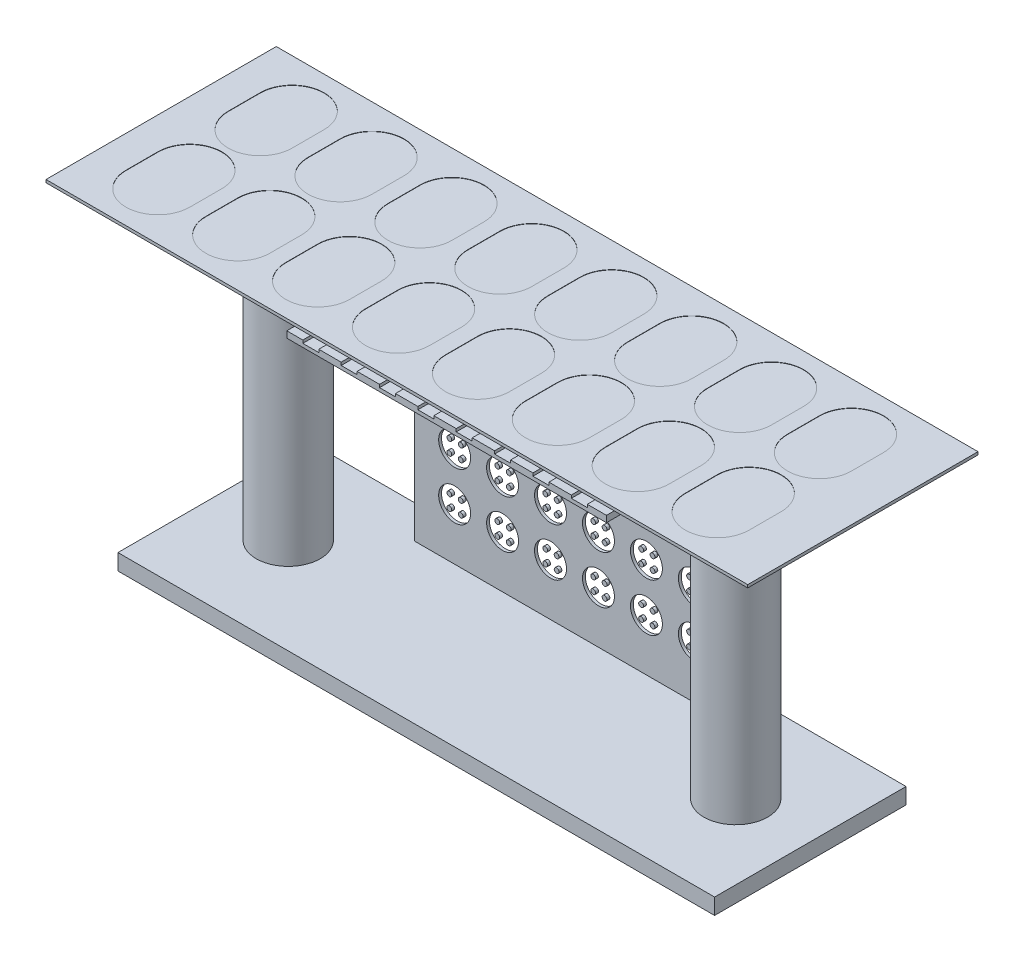
SolidWorks part; units mm, degrees
ref_plane "Front Plane" through (0, 0, 0) normal (0, 0, 1) x (1, 0, 0)
ref_plane "Top Plane" through (0, 0, 0) normal (0, 1, 0) x (1, 0, 0)
ref_plane "Right Plane" through (0, 0, 0) normal (1, 0, 0) x (0, 0, -1)
sketch "Sketch3" plane through (0, 0, 0) normal (0, 0, 1) x (1, 0, 0)
  line L1 (-5000, 4000) -> (5000, 4000)
  line L2 (-5000, 4000) -> (-5000, -4000)
  line L3 (-5000, -4000) -> (5000, -4000)
  line L4 (5000, 4000) -> (5000, -4000)
  line L5 (-5000, 4000) -> (5000, -4000) construction
  line L6 (-5000, -4000) -> (5000, 4000) construction
  point P0 (0, 0)
  dimension "D1" = 8000
  dimension "D2" = 10000
extrude "Boss-Extrude1" add sketch "Sketch3" along normal blind 90
ref_plane "Plane2" through (0, 4000, 0) normal (0, 1, 0) x (1, 0, 0)
sketch "Sketch6" plane through (0, 4000, 0) normal (0, 1, 0) x (1, 0, 0)
  line L0 (-5000, -90) -> (-5000, -4090)
  line L1 (-5000, -4090) -> (5000, -4090)
  line L2 (5000, -4090) -> (5000, -90)
  line L3 (5000, -90) -> (-5000, -90)
  dimension "D1" = 4000
extrude "Boss-Extrude2" add sketch "Sketch6" along normal blind 200 separate body
sketch "Sketch7" plane through (0, 0, 90) normal (0, 0, 1) x (1, 0, 0)
  line L0 (-5000, 4000) -> (-5000, -4000) construction
  line L1 (-3750, 2623.5986) -> (-3750, 1123.5986) construction
  circle A0 centre (-3750, 2623.5986) radius 500
  circle A1 centre (-3915.8517, 2823.5986) radius 75
  circle A2 centre (-3559.1798, 2823.5986) radius 75
  circle A3 centre (-3559.1798, 2423.5986) radius 75
  circle A4 centre (-3915.8517, 2423.5986) radius 75
  circle A5 centre (-2250, 2623.5986) radius 500
  circle A6 centre (-2415.8517, 2423.5986) radius 75
  circle A7 centre (-2059.1798, 2823.5986) radius 75
  circle A8 centre (-2059.1798, 2423.5986) radius 75
  circle A9 centre (-2415.8517, 2823.5986) radius 75
  circle A10 centre (-750, 2623.5986) radius 500
  circle A11 centre (-915.8517, 2423.5986) radius 75
  circle A12 centre (-559.1798, 2823.5986) radius 75
  circle A13 centre (-559.1798, 2423.5986) radius 75
  circle A14 centre (-915.8517, 2823.5986) radius 75
  circle A15 centre (750, 2623.5986) radius 500
  circle A16 centre (584.1483, 2423.5986) radius 75
  circle A17 centre (940.8202, 2823.5986) radius 75
  circle A18 centre (940.8202, 2423.5986) radius 75
  circle A19 centre (584.1483, 2823.5986) radius 75
  circle A20 centre (2250, 2623.5986) radius 500
  circle A21 centre (2084.1483, 2423.5986) radius 75
  circle A22 centre (2440.8202, 2823.5986) radius 75
  circle A23 centre (2440.8202, 2423.5986) radius 75
  circle A24 centre (2084.1483, 2823.5986) radius 75
  circle A25 centre (3750, 2623.5986) radius 500
  circle A26 centre (3584.1483, 2423.5986) radius 75
  circle A27 centre (3940.8202, 2823.5986) radius 75
  circle A28 centre (3940.8202, 2423.5986) radius 75
  circle A29 centre (3584.1483, 2823.5986) radius 75
  circle A30 centre (-2250, 1123.5986) radius 500
  circle A31 centre (-2415.8517, 923.5986) radius 75
  circle A32 centre (-2059.1798, 1323.5986) radius 75
  circle A33 centre (-2059.1798, 923.5986) radius 75
  circle A34 centre (-2415.8517, 1323.5986) radius 75
  circle A35 centre (-750, 1123.5986) radius 500
  circle A36 centre (-915.8517, 923.5986) radius 75
  circle A37 centre (-559.1798, 1323.5986) radius 75
  circle A38 centre (-559.1798, 923.5986) radius 75
  circle A39 centre (-915.8517, 1323.5986) radius 75
  circle A40 centre (750, 1123.5986) radius 500
  circle A41 centre (584.1483, 923.5986) radius 75
  circle A42 centre (940.8202, 1323.5986) radius 75
  circle A43 centre (940.8202, 923.5986) radius 75
  circle A44 centre (584.1483, 1323.5986) radius 75
  circle A45 centre (2250, 1123.5986) radius 500
  circle A46 centre (2084.1483, 923.5986) radius 75
  circle A47 centre (2440.8202, 1323.5986) radius 75
  circle A48 centre (2440.8202, 923.5986) radius 75
  circle A49 centre (2084.1483, 1323.5986) radius 75
  circle A50 centre (3750, 1123.5986) radius 500
  circle A51 centre (3584.1483, 923.5986) radius 75
  circle A52 centre (3940.8202, 1323.5986) radius 75
  circle A53 centre (3940.8202, 923.5986) radius 75
  circle A54 centre (3584.1483, 1323.5986) radius 75
  circle A55 centre (-2250, -376.4014) radius 500
  circle A56 centre (-2415.8517, -576.4014) radius 75
  circle A57 centre (-2059.1798, -176.4014) radius 75
  circle A58 centre (-2059.1798, -576.4014) radius 75
  circle A59 centre (-2415.8517, -176.4014) radius 75
  circle A60 centre (-750, -376.4014) radius 500
  circle A61 centre (-915.8517, -576.4014) radius 75
  circle A62 centre (-559.1798, -176.4014) radius 75
  circle A63 centre (-559.1798, -576.4014) radius 75
  circle A64 centre (-915.8517, -176.4014) radius 75
  circle A65 centre (750, -376.4014) radius 500
  circle A66 centre (584.1483, -576.4014) radius 75
  circle A67 centre (940.8202, -176.4014) radius 75
  circle A68 centre (940.8202, -576.4014) radius 75
  circle A69 centre (584.1483, -176.4014) radius 75
  circle A70 centre (2250, -376.4014) radius 500
  circle A71 centre (2084.1483, -576.4014) radius 75
  circle A72 centre (2440.8202, -176.4014) radius 75
  circle A73 centre (2440.8202, -576.4014) radius 75
  circle A74 centre (2084.1483, -176.4014) radius 75
  circle A75 centre (3750, -376.4014) radius 500
  circle A76 centre (3584.1483, -576.4014) radius 75
  circle A77 centre (3940.8202, -176.4014) radius 75
  circle A78 centre (3940.8202, -576.4014) radius 75
  circle A79 centre (3584.1483, -176.4014) radius 75
  circle A80 centre (-2250, -1876.4014) radius 500
  circle A81 centre (-2415.8517, -2076.4014) radius 75
  circle A82 centre (-2059.1798, -1676.4014) radius 75
  circle A83 centre (-2059.1798, -2076.4014) radius 75
  circle A84 centre (-2415.8517, -1676.4014) radius 75
  circle A85 centre (-750, -1876.4014) radius 500
  circle A86 centre (-915.8517, -2076.4014) radius 75
  circle A87 centre (-559.1798, -1676.4014) radius 75
  circle A88 centre (-559.1798, -2076.4014) radius 75
  circle A89 centre (-915.8517, -1676.4014) radius 75
  circle A90 centre (750, -1876.4014) radius 500
  circle A91 centre (584.1483, -2076.4014) radius 75
  circle A92 centre (940.8202, -1676.4014) radius 75
  circle A93 centre (940.8202, -2076.4014) radius 75
  circle A94 centre (584.1483, -1676.4014) radius 75
  circle A95 centre (2250, -1876.4014) radius 500
  circle A96 centre (2084.1483, -2076.4014) radius 75
  circle A97 centre (2440.8202, -1676.4014) radius 75
  circle A98 centre (2440.8202, -2076.4014) radius 75
  circle A99 centre (2084.1483, -1676.4014) radius 75
  circle A100 centre (3750, -1876.4014) radius 500
  circle A101 centre (3584.1483, -2076.4014) radius 75
  circle A102 centre (3940.8202, -1676.4014) radius 75
  circle A103 centre (3940.8202, -2076.4014) radius 75
  circle A104 centre (3584.1483, -1676.4014) radius 75
  circle A105 centre (-3750, 1123.5986) radius 500
  circle A106 centre (-3915.8517, 923.5986) radius 75
  circle A107 centre (-3559.1798, 1323.5986) radius 75
  circle A108 centre (-3559.1798, 923.5986) radius 75
  circle A109 centre (-3915.8517, 1323.5986) radius 75
  circle A110 centre (-3750, -376.4014) radius 500
  circle A111 centre (-3915.8517, -576.4014) radius 75
  circle A112 centre (-3559.1798, -176.4014) radius 75
  circle A113 centre (-3559.1798, -576.4014) radius 75
  circle A114 centre (-3915.8517, -176.4014) radius 75
  circle A115 centre (-3750, -1876.4014) radius 500
  circle A116 centre (-3915.8517, -2076.4014) radius 75
  circle A117 centre (-3559.1798, -1676.4014) radius 75
  circle A118 centre (-3559.1798, -2076.4014) radius 75
  circle A119 centre (-3915.8517, -1676.4014) radius 75
  dimension "D5" = 150
  dimension "D6" = 150
  dimension "D7" = 150
  dimension "D8" = 150
  dimension "D10" = 1000
  dimension "D1" = 200
  dimension "D2" = 200
  dimension "D3" = 200
  dimension "D4" = 200
  dimension "D9" = 1250
  dimension "D13" = 1500
  dimension "D11" = 6
  dimension "D12" = 4
extrude "Cut-Extrude4" cut sketch "Sketch7" against normal through all contours A0 | A4 | A3 | A2 | A1
pattern_linear "LPattern1" count 6 spacing 1500 along (1, 0, 0) count 4 spacing 1500 along (0, -1, 0) of "Cut-Extrude4"
ref_plane "Plane3" through (0, -4000, 0) normal (0, 1, 0) x (1, 0, 0)
sketch "Sketch11" plane through (0, -4000, 0) normal (0, 1, 0) x (1, 0, 0)
  line L0 (-5000, -90) -> (-5000, -4090) construction
  line L1 (5000, -4090) -> (5000, -90) construction
  circle A0 centre (7000, -2045) radius 1000
  circle A1 centre (-7000, -2045) radius 1000
  dimension "D3" = 2000
  dimension "D4" = 2000
  dimension "D1" = 2000
  dimension "D2" = 2000
extrude "Boss-Extrude3" add sketch "Sketch11" along normal blind 10000 separate body
sketch "Sketch13" plane through (0, -4000, 0) normal (0, 1, 0) x (1, 0, 0)
  line L1 (-9333.4186, 950.2518) -> (9333.4186, 950.2518)
  line L2 (-9333.4186, 950.2518) -> (-9333.4186, -5040.2518)
  line L3 (-9333.4186, -5040.2518) -> (9333.4186, -5040.2518)
  line L4 (9333.4186, 950.2518) -> (9333.4186, -5040.2518)
  line L5 (-9333.4186, 950.2518) -> (9333.4186, -5040.2518) construction
  line L6 (-9333.4186, -5040.2518) -> (9333.4186, 950.2518) construction
  point P0 (0, -2045)
extrude "Boss-Extrude4" add sketch "Sketch13" along normal blind 500
sketch "Sketch14" plane through (0, 4200, 0) normal (0, 1, 0) x (1, 0, 0)
  line L0 (5000, -90) -> (-5000, -90) construction
  line L1 (-4500, -90) -> (-4000, -90)
  line L2 (-4500, -90) -> (-4500, -4090)
  line L3 (-4500, -4090) -> (-4000, -4090)
  line L4 (-4000, -90) -> (-4000, -4090)
  line L5 (-5000, -4090) -> (5000, -4090) construction
  line L6 (-5000, -90) -> (-5000, -4090) construction
  dimension "D1" = 500
  dimension "D2" = 500
extrude "Cut-Extrude5" cut sketch "Sketch14" against normal blind 90 contours L2 L3 L4 L1
pattern_linear "LPattern2" count 8 spacing 1200 along (1, 0, 0) of "Cut-Extrude5"
sketch "Sketch17" plane through (0, 6000, 0) normal (0, 1, 0) x (1, 0, 0)
  line L1 (-10977.0173, 1557.277) -> (10977.0173, 1557.277)
  line L2 (-10977.0173, 1557.277) -> (-10977.0173, -5647.277)
  line L3 (-10977.0173, -5647.277) -> (10977.0173, -5647.277)
  line L4 (10977.0173, 1557.277) -> (10977.0173, -5647.277)
  line L5 (-10977.0173, 1557.277) -> (10977.0173, -5647.277) construction
  line L6 (-10977.0173, -5647.277) -> (10977.0173, 1557.277) construction
  point P0 (0, -2045)
  dimension "D1" = 7204.554
extrude "Boss-Extrude5" add sketch "Sketch17" along normal blind 90
sketch "Sketch19" plane through (0, 6090, 0) normal (0, 1, 0) x (1, 0, 0)
  line L0 (-8977.0173, -4146.6362) -> (-8977.0173, -3146.6362) construction
  line L1 (-9977.0173, -4146.6362) -> (-9977.0173, -3146.6362)
  line L2 (-7977.0173, -4146.6362) -> (-7977.0173, -3146.6362)
  line L3 (-10977.0173, 1557.277) -> (-10977.0173, -5647.277) construction
  arc A0 (-9977.0173, -4146.6362) -> (-7977.0173, -4146.6362) centre (-8977.0173, -4146.6362) ccw
  arc A1 (-7977.0173, -3146.6362) -> (-9977.0173, -3146.6362) centre (-8977.0173, -3146.6362) ccw
  point P2 (-8977.0173, -3646.6362)
  dimension "D1" = 2000
  dimension "D2" = 1000
  dimension "D3" = 1000
extrude "Cut-Extrude6" cut sketch "Sketch19" against normal blind 10 contours A1 L1 A0 L2
pattern_linear "LPattern3" count 8 spacing 2500 along (1, 0, 0) count 2 spacing 3200 along (0, 0, -1) of "Cut-Extrude6"
